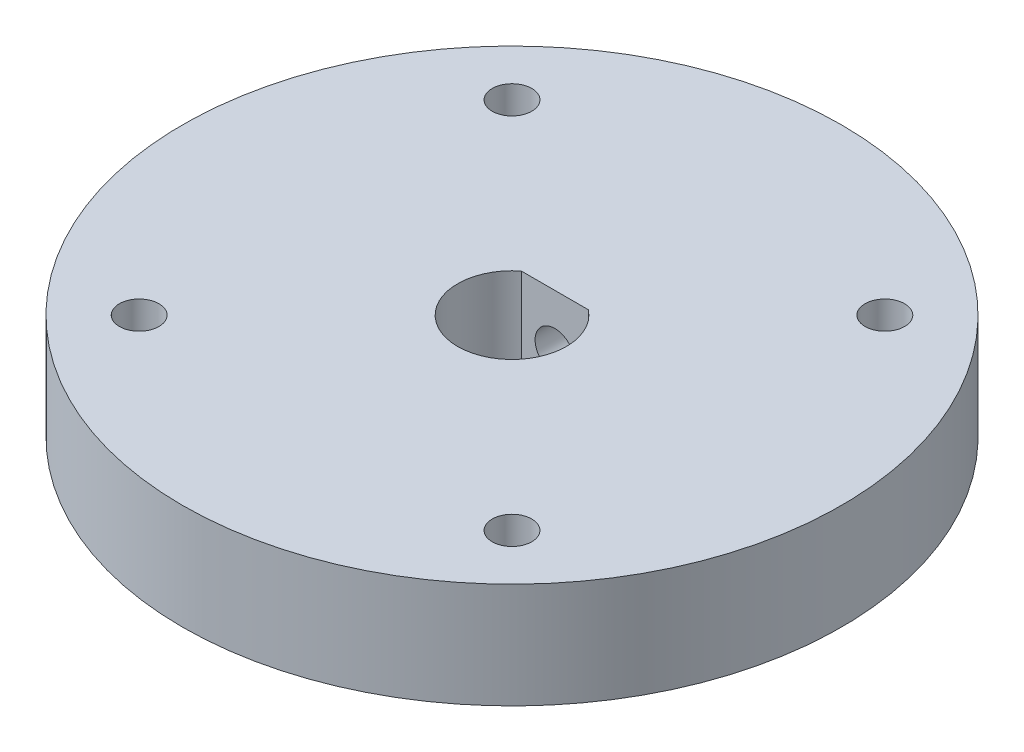
SolidWorks part; units mm, degrees
ref_plane "Front Plane" through (0, 0, 0) normal (0, 0, 1) x (1, 0, 0)
ref_plane "Top Plane" through (0, 0, 0) normal (0, 1, 0) x (1, 0, 0)
ref_plane "Right Plane" through (0, 0, 0) normal (1, 0, 0) x (0, 0, -1)
sketch "Sketch1" plane through (0, 0, 0) normal (0, 1, 0) x (1, 0, 0)
  line L0 (2.5403, 3.25) -> (-2.5403, 3.25)
  line L1 (0, 0) -> (-14.1421, -14.1421) construction
  line L2 (0, 0) -> (0, -14.7733) construction
  circle A0 centre (0, 0) radius 25
  arc A1 (-2.5403, 3.25) -> (2.5403, 3.25) centre (0, 0) ccw
  circle A2 centre (-14.1421, -14.1421) radius 1.5
  circle A3 centre (-14.1421, 14.1421) radius 1.5
  circle A4 centre (14.1421, 14.1421) radius 1.5
  circle A5 centre (14.1421, -14.1421) radius 1.5
  point P18 (0, 0)
  dimension "D1" = 50
  dimension "D3" = 3
  dimension "D2" = 45
  dimension "D4" = 20
  dimension "D5" = 4
extrude "Boss-Extrude1" add sketch "Sketch1" along normal blind 8
sketch "Sketch2" plane through (0, 0, -3.25) normal (0, 0, 1) x (1, 0, 0)
  line L0 (2.5403, 0) -> (-2.5403, 0) construction
  line L1 (2.5403, 8) -> (-2.5403, 8) construction
  line L2 (2.5403, 0) -> (-2.5403, 0)
  line L3 (2.5403, 8) -> (-2.5403, 8)
  line L4 (0, 0) -> (0, 8) construction
  circle A0 centre (0, 4) radius 1.5
  dimension "D1" = 3
extrude "Cut-Extrude1" cut sketch "Sketch2" against normal blind 35 contours A0 L4 | L4 A0
ref_plane "Plane1" through (0, 0, -24) normal (0, 0, 1) x (1, 0, 0)
sketch "Sketch3" plane through (0, 0, -24) normal (0, 0, 1) x (1, 0, 0)
  line L4 (-2.5403, 0) -> (2.5403, 0)
  line L5 (2.5403, 0) -> (2.5403, 8)
  line L6 (2.5403, 8) -> (-2.5403, 8)
  line L7 (-2.5403, 8) -> (-2.5403, 0)
  line L8 (-2.5403, 0) -> (2.5403, 0)
  line L9 (2.5403, 0) -> (2.5403, 8)
  line L10 (2.5403, 8) -> (-2.5403, 8)
  line L11 (-2.5403, 8) -> (-2.5403, 0)
  circle A1 centre (0, 4) radius 2.5403
  dimension "D1" = 0
extrude "Cut-Extrude3" cut sketch "Sketch3" against normal blind 35 and the other way blind 2 contours A1
